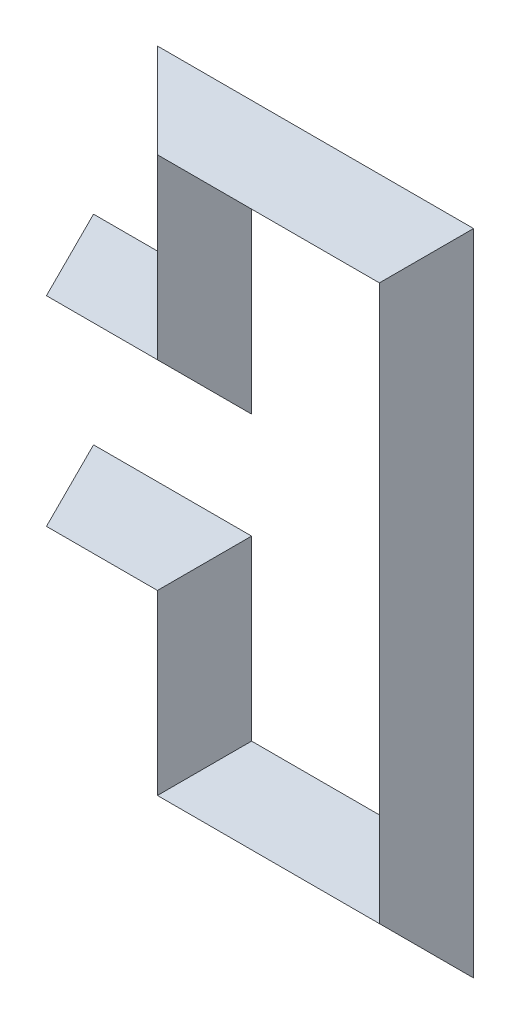
SolidWorks part; units mm, degrees
ref_plane "정면" through (0, 0, 0) normal (0, 0, 1) x (1, 0, 0)
ref_plane "윗면" through (0, 0, 0) normal (0, 1, 0) x (1, 0, 0)
ref_plane "우측면" through (0, 0, 0) normal (1, 0, 0) x (0, 0, -1)
sketch "스케치2" plane through (0, 0, 0) normal (0, 0, 1) x (1, 0, 0)
  line L0 (0, 0) -> (50, 0)
  line L1 (50, 0) -> (50, 80)
  line L2 (50, 80) -> (150, 80)
  line L3 (150, 80) -> (150, -170)
  line L4 (150, -170) -> (50, -170)
  line L5 (50, -170) -> (50, -90)
  line L6 (50, -90) -> (0, -90)
  dimension "D1" = 50
  dimension "D2" = 80
  dimension "D3" = 100
  dimension "D4" = 250
sketch "스케치3" plane through (0, 0, 0) normal (1, 0, 0) x (0, 0, -1)
  line L0 (21.2132, 0) -> (0, -21.2132)
  line L1 (21.2132, 0) -> (0, 21.2132)
  line L2 (0, -21.2132) -> (-21.2132, 0)
  line L3 (0, 21.2132) -> (-21.2132, 0)
  line L4 (21.2132, 0) -> (-21.2132, 0) construction
  line L5 (0, -21.2132) -> (0, 21.2132) construction
  point P1 (0, 0)
  dimension "D1" = 30
sweep "스윕1" add profiles "스케치3" path "스케치2"
